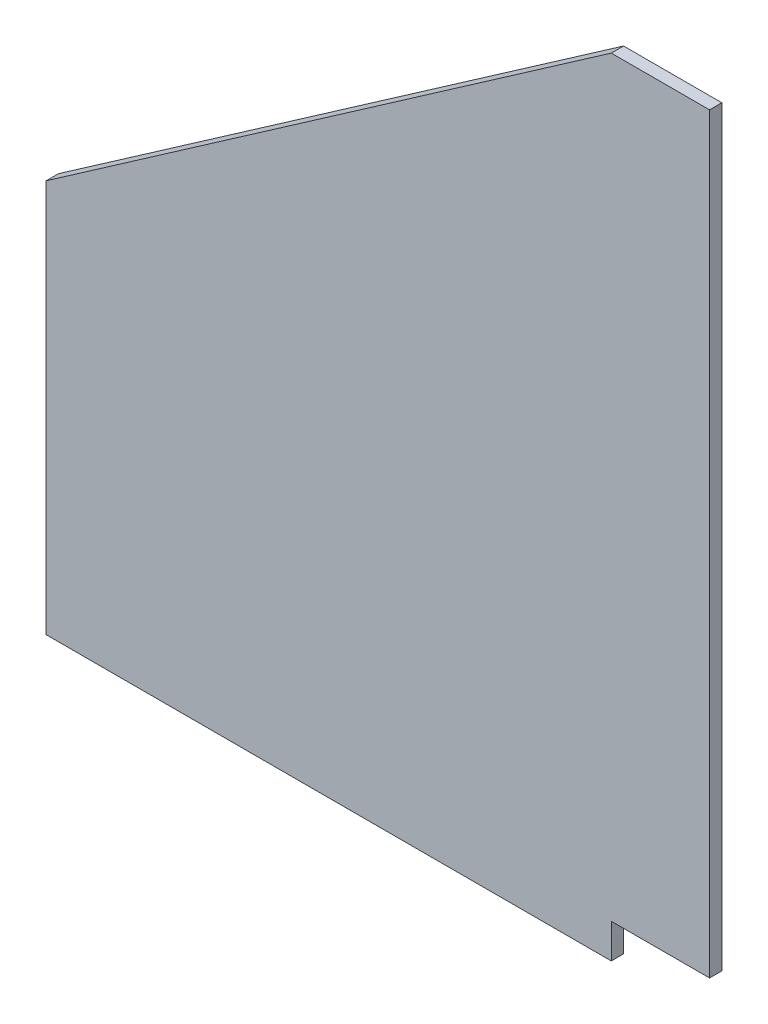
SolidWorks part; units mm, degrees
material "A-Glass Fiber"
ref_plane "Front Plane" through (0, 0, 0) normal (0, 0, 1) x (1, 0, 0)
ref_plane "Top Plane" through (0, 0, 0) normal (0, 1, 0) x (1, 0, 0)
ref_plane "Right Plane" through (0, 0, 0) normal (1, 0, 0) x (0, 0, -1)
sketch "Sketch1" plane through (0, 0, 0) normal (0, 0, 1) x (1, 0, 0)
  line L0 (0, 0) -> (0, 194.31)
  line L1 (0, 194.31) -> (-25.4, 194.31)
  line L3 (-171.45, -8.89) -> (-25.4, -8.89)
  line L4 (-25.4, -8.89) -> (-25.4, 0)
  line L5 (-25.4, 0) -> (0, 0)
  line L6 (-171.45, -8.89) -> (-171.45, 92.71)
  line L7 (-171.45, 92.71) -> (-25.4, 194.31)
  dimension "D1" = 194.31
  dimension "D2" = 146.05
  dimension "D3" = 25.4
  dimension "D4" = 203.2
  dimension "D5" = 25.4
  dimension "D6" = 101.6
extrude "Boss-Extrude1" add sketch "Sketch1" along normal blind 3.175
